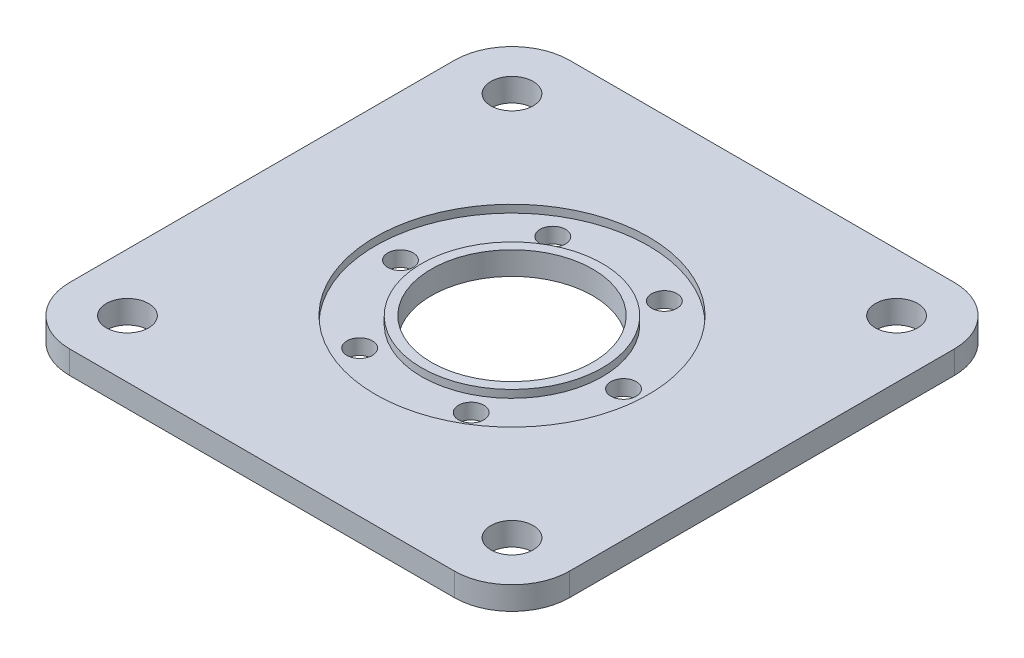
SolidWorks part; units mm, degrees
ref_plane "Front Plane" through (0, 0, 0) normal (0, 0, 1) x (1, 0, 0)
ref_plane "Top Plane" through (0, 0, 0) normal (0, 1, 0) x (1, 0, 0)
ref_plane "Right Plane" through (0, 0, 0) normal (1, 0, 0) x (0, 0, -1)
sketch "Sketch1" plane through (0, 0, 0) normal (0, 1, 0) x (1, 0, 0)
  line L1 (-50, -65) -> (50, -65)
  line L2 (-65, -50) -> (-65, 50)
  line L3 (-50, 65) -> (50, 65)
  line L4 (65, -50) -> (65, 50)
  line L5 (-65, -65) -> (65, 65) construction
  line L6 (-65, 65) -> (65, -65) construction
  arc A0 (-50, -65) -> (-65, -50) centre (-50, -50) cw
  arc A1 (-65, 50) -> (-50, 65) centre (-50, 50) cw
  arc A2 (65, 50) -> (50, 65) centre (50, 50) ccw
  arc A3 (50, -65) -> (65, -50) centre (50, -50) ccw
  circle A4 centre (0, 0) radius 21
  point P0 (0, 0)
  dimension "D1" = 15
  dimension "D2" = 42
  dimension "D3" = 130
extrude "Boss-Extrude1" add sketch "Sketch1" along normal blind 6
sketch "Sketch2" plane through (0, 6, 0) normal (0, 1, 0) x (1, 0, 0)
  circle A0 centre (0, 0) radius 23.5
  circle A1 centre (0, 0) radius 35.5
  dimension "D1" = 47
  dimension "D2" = 12
extrude "Cut-Extrude1" cut sketch "Sketch2" against normal blind 2
sketch "Sketch3" plane through (0, 6, 0) normal (0, 1, 0) x (1, 0, 0)
  line L1 (-50, -50) -> (50, -50) construction
  line L2 (-50, -50) -> (-50, 50) construction
  line L3 (-50, 50) -> (50, 50) construction
  line L4 (50, -50) -> (50, 50) construction
  line L5 (-50, -50) -> (50, 50) construction
  line L6 (-50, 50) -> (50, -50) construction
  circle A0 centre (-50, 50) radius 5.5
  circle A1 centre (50, 50) radius 5.5
  circle A2 centre (50, -50) radius 5.5
  circle A3 centre (-50, -50) radius 5.5
  point P0 (0, 0)
  dimension "D2" = 11
  dimension "D1" = 100
extrude "Cut-Extrude2" cut sketch "Sketch3" against normal through all both and the other way through all
sketch "Sketch4" plane through (0, 4, 0) normal (0, 1, 0) x (1, 0, 0)
  point P0 (-29, 0)
  dimension "D1" = 29
hole_wizard "M6 Clearance Hole1" positions "3DSketch1" profile "Sketch5" hole size "M6" standard "ISO" end condition up to next
sketch3d "3DSketch1"
  point P0 (-29, 4, 0)
sketch "Sketch5" plane through (-29, 4, 0) normal (1, 0, 0) x (0, 0, 1)
  line L0 (0, 0) -> (0, 4)
  line L1 (0, 4) -> (3.3, 4)
  line L2 (3.3, 4) -> (3.3, 0)
  line L5 (3.3, 0) -> (0, 0)
  line L11 (0, -6.35) -> (0, 107.95) construction
  dimension "Thru Hole Dia." = 6.6
  dimension "Thru Hole Depth" = 4
pattern_circular "CirPattern1" count 6 over 360 about axis through (0, 0, 0) along (0, 1, 0) of "M6 Clearance Hole1"
